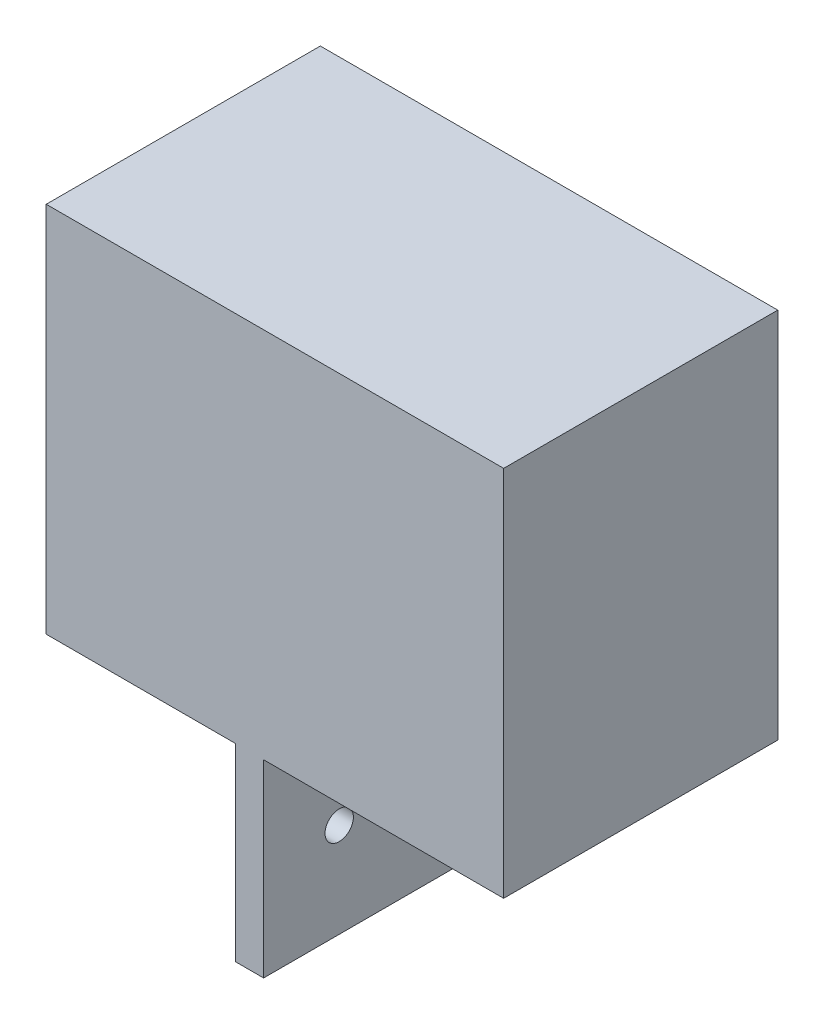
SolidWorks part; units mm, degrees
ref_plane "Front Plane" through (0, 0, 0) normal (0, 0, 1) x (1, 0, 0)
ref_plane "Top Plane" through (0, 0, 0) normal (0, 1, 0) x (1, 0, 0)
ref_plane "Right Plane" through (0, 0, 0) normal (1, 0, 0) x (0, 0, -1)
sketch "Sketch2" plane through (0, 0, 0) normal (0, 0, 1) x (1, 0, 0)
  line L1 (0, 0) -> (42.418, 0)
  line L2 (0, 0) -> (0, 42.418)
  line L3 (0, 42.418) -> (42.418, 42.418)
  line L4 (42.418, 0) -> (42.418, 42.418)
  line L5 (-3.81, 46.228) -> (44.958, 46.228)
  line L6 (-3.81, 46.228) -> (-3.81, -3.81)
  line L7 (-3.81, -3.81) -> (44.958, -3.81)
  line L8 (44.958, 46.228) -> (44.958, -3.81)
  dimension "D1" = 42.418
  dimension "D2" = 42.418
  dimension "D3" = 3.81
  dimension "D4" = 3.81
  dimension "D5" = 2.54
  dimension "D6" = 3.81
extrude "Boss-Extrude1" add sketch "Sketch2" along normal blind 34.29
sketch "Sketch4" plane through (0, 0, 34.29) normal (0, 0, 1) x (1, 0, 0)
  line L1 (-3.81, 46.228) -> (44.958, 46.228)
  line L2 (-3.81, 46.228) -> (-3.81, -3.81)
  line L3 (-3.81, -3.81) -> (44.958, -3.81)
  line L4 (44.958, 46.228) -> (44.958, -3.81)
extrude "Boss-Extrude2" add sketch "Sketch4" along normal blind 2.54
sketch "Sketch5" plane through (0, 0, 0) normal (0, 0, -1) x (-1, 0, 0)
  line L6 (3.81, -3.81) -> (-44.958, -3.81) construction
  line L7 (-12.7, -3.81) -> (-8.89, -3.81)
  line L8 (-12.7, -3.81) -> (-12.7, -29.21)
  line L9 (-12.7, -29.21) -> (-8.89, -29.21)
  line L10 (-8.89, -3.81) -> (-8.89, -29.21)
  line L11 (3.81, 46.228) -> (3.81, -3.81) construction
  dimension "D1" = 12.7
  dimension "D2" = 3.81
  dimension "D3" = 25.4
extrude "Boss-Extrude3" add sketch "Sketch5" against normal up to surface (36.83 mm away) up to face at (20.574, 21.209, 36.83)
sketch "Sketch6" plane through (0, 0, 0) normal (0, 0, -1) x (-1, 0, 0)
  line L0 (-44.958, 46.228) -> (3.81, 46.228) construction
  line L1 (3.81, -3.81) -> (16.51, -3.81)
  line L2 (3.81, -3.81) -> (3.81, 46.228)
  line L3 (3.81, 46.228) -> (16.51, 46.228)
  line L4 (16.51, -3.81) -> (16.51, 46.228)
  dimension "D1" = 0
  dimension "D2" = 12.7
extrude "Boss-Extrude4" add sketch "Sketch6" against normal up to surface (36.83 mm away) up to face at (15.6845, 2.3495, 36.83)
sketch "Sketch7" plane through (12.7, 0, 0) normal (1, 0, 0) x (0, 0, -1)
  line L0 (-36.83, -29.21) -> (0, -29.21) construction
  line L1 (0, -3.81) -> (0, -29.21) construction
  line L2 (-36.83, -3.81) -> (-36.83, -29.21) construction
  circle A0 centre (-26.67, -16.51) radius 1.905
  circle A1 centre (-10.16, -16.51) radius 1.905
  dimension "D1" = 3.81
  dimension "D2" = 3.81
  dimension "D3" = 12.7
  dimension "D4" = 12.7
  dimension "D5" = 10.16
  dimension "D6" = 10.16
extrude "Cut-Extrude1" cut sketch "Sketch7" against normal through all
